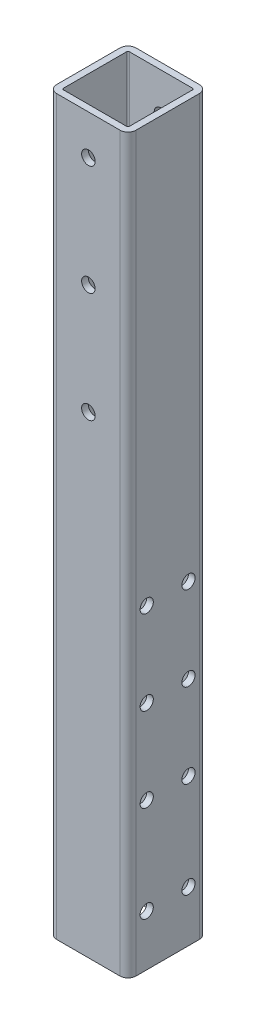
SolidWorks part; units mm, degrees
material "Alloy Steel"
ref_plane "Front Plane" through (0, 0, 0) normal (0, 0, 1) x (1, 0, 0)
ref_plane "Top Plane" through (0, 0, 0) normal (0, 1, 0) x (1, 0, 0)
ref_plane "Right Plane" through (0, 0, 0) normal (1, 0, 0) x (0, 0, -1)
sketch "Sketch1" plane through (0, 0, 0) normal (0, 1, 0) x (1, 0, 0)
  line L0 (-15.875, 15.875) -> (-15.875, -15.875)
  line L1 (-19.05, 19.05) -> (19.05, 19.05)
  line L2 (-19.05, 19.05) -> (-19.05, -19.05)
  line L3 (-19.05, -19.05) -> (19.05, -19.05)
  line L4 (19.05, 19.05) -> (19.05, -19.05)
  line L5 (-19.05, 19.05) -> (19.05, -19.05) construction
  line L6 (-19.05, -19.05) -> (19.05, 19.05) construction
  line L7 (-15.875, -15.875) -> (15.875, -15.875)
  line L8 (15.875, 15.875) -> (15.875, -15.875)
  line L9 (-15.875, 15.875) -> (15.875, 15.875)
  point P0 (0, 0)
  dimension "D2" = 38.1
  dimension "D3" = 38.1
  dimension "D1" = 3.175
extrude "Boss-Extrude1" add sketch "Sketch1" along normal mid plane 352.425
fillet "Fillet1" radius 3.81 4 edges at (-19.05, 0, -19.05) (-19.05, 0, 19.05) (19.05, 0, -19.05) (19.05, 0, 19.05)
fillet "Fillet2" radius 0.635 4 edges at (15.875, 0, 15.875) (15.875, 0, -15.875) (-15.875, 0, 15.875) (-15.875, 0, -15.875)
sketch "Sketch2" plane through (0, 0, 19.05) normal (0, 0, 1) x (1, 0, 0)
  line L0 (0, 176.2125) -> (0, -176.2125) construction
  line L1 (-15.24, 176.2125) -> (15.24, 176.2125) construction
  line L2 (-15.24, -176.2125) -> (15.24, -176.2125) construction
  circle A0 centre (0, 157.1625) radius 3.2639
  circle A1 centre (0, 104.1625) radius 3.2639
  circle A2 centre (0, 51.1625) radius 3.2639
  dimension "D1" = 6.5278
  dimension "D2" = 19.05
  dimension "D3" = 53
  dimension "D4" = 53
extrude "Cut-Extrude1" cut sketch "Sketch2" against normal through all both and the other way through all
sketch "Sketch5" plane through (19.05, 0, 0) normal (1, 0, 0) x (0, 0, -1)
  line L0 (-10.05, 176.2125) -> (-10.05, -176.2125) construction
  line L1 (-15.24, 176.2125) -> (15.24, 176.2125) construction
  line L2 (-15.24, -176.2125) -> (15.24, -176.2125) construction
  line L3 (10.05, -176.2125) -> (10.05, 176.2125) construction
  line L4 (-19.05, -176.2125) -> (-19.05, 176.2125) construction
  line L5 (19.05, 176.2125) -> (19.05, -176.2125) construction
  circle A0 centre (-10.05, -151.6875) radius 3.175
  circle A1 centre (-10.05, -24.4875) radius 3.175
  circle A2 centre (-10.05, -105.4875) radius 3.175
  circle A3 centre (-10.05, -64.9875) radius 3.175
  circle A4 centre (10.05, -151.6875) radius 3.175
  circle A5 centre (10.05, -24.4875) radius 3.175
  circle A6 centre (10.05, -105.4875) radius 3.175
  circle A7 centre (10.05, -64.9875) radius 3.175
  point P28 (0, 0)
  point P29 (0, 0)
  point P30 (0, 0)
  point P31 (0, 0)
  point P32 (-10.05, -108.0627)
  point P33 (-10.05, -98.7403)
  point P34 (-10.05, -78.9484)
  point P35 (-10.05, -43.4361)
  dimension "D3" = 6.35
  dimension "D1" = 9
  dimension "D2" = 9
  dimension "D4" = 24.525
  dimension "D5" = 46.2
  dimension "D6" = 40.5
  dimension "D7" = 40.5
extrude "Cut-Extrude3" cut sketch "Sketch5" against normal through all
